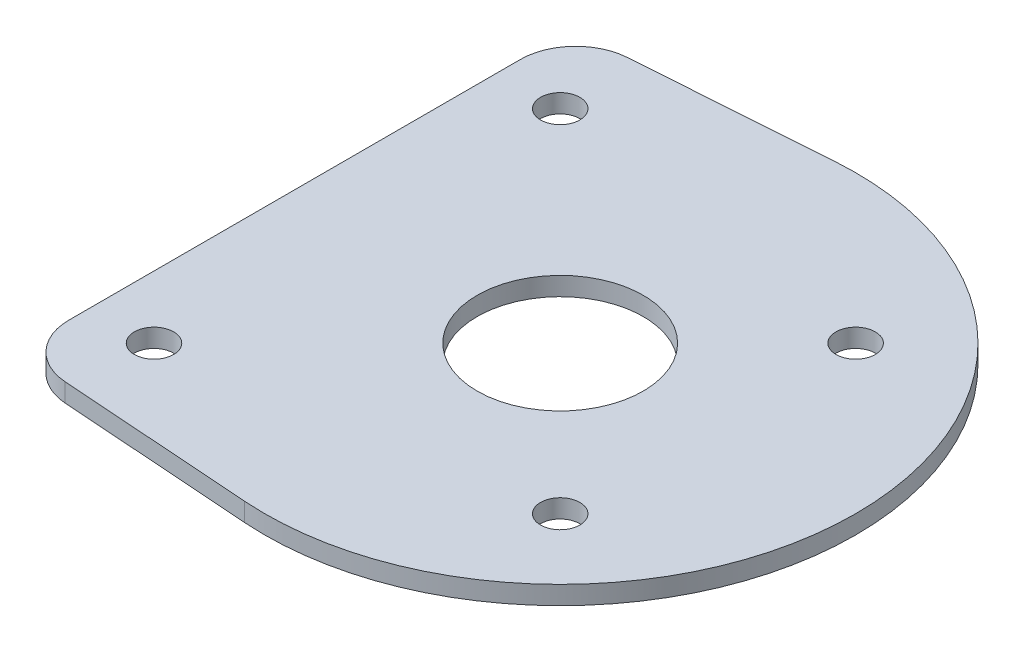
SolidWorks part; units mm, degrees
material "6061 Alloy"
ref_plane "Front Plane" through (0, 0, 0) normal (0, 0, 1) x (1, 0, 0)
ref_plane "Top Plane" through (0, 0, 0) normal (0, 1, 0) x (1, 0, 0)
ref_plane "Right Plane" through (0, 0, 0) normal (1, 0, 0) x (0, 0, -1)
sketch "Sketch1" plane through (0, 0, 0) normal (0, 1, 0) x (1, 0, 0)
  line L0 (87.0156, 23.109) -> (-1.4599, 13.6381) construction
  line L1 (-17.9605, -17.9605) -> (17.9605, -17.9605) construction
  line L2 (-17.9605, -17.9605) -> (-17.9605, 17.9605) construction
  line L3 (-17.9605, 17.9605) -> (17.9605, 17.9605) construction
  line L4 (17.9605, -17.9605) -> (17.9605, 17.9605) construction
  line L5 (-17.9605, -17.9605) -> (17.9605, 17.9605) construction
  line L6 (-17.9605, 17.9605) -> (17.9605, -17.9605) construction
  line L7 (87.0156, -23.109) -> (-1.4599, -13.6381) construction
  line L8 (85.8846, 50.6719) -> (-3.1541, 44.338)
  line L9 (85.8846, -50.6719) -> (-3.1541, -44.338)
  circle A1 centre (0, 0) radius 13.716 construction
  circle A2 centre (89.4893, 0) radius 23.241 construction
  circle A3 centre (89.4893, 0) radius 14.2812
  circle A4 centre (0, 0) radius 19.177
  arc A5 (-3.1541, 44.338) -> (-3.1541, -44.338) centre (0, 0) ccw
  arc A6 (85.8846, 50.6719) -> (85.8846, -50.6719) centre (89.4893, 0) cw
  point P0 (0, 0)
  point P2 (140.2893, 0)
  point P27 (-44.45, 0)
  dimension "D1" = 50.8
  dimension "D2" = 27.432
  dimension "D3" = 46.482
  dimension "D5" = 28.5623
  dimension "D6" = 38.354
  dimension "D4" = 89.4893
  dimension "D7" = 44.45
  dimension "D8" = 50.8
extrude "Boss-Extrude1" add sketch "Sketch1" along normal blind 3.175
hole_wizard "#10 Clearance Hole1" positions "Sketch2" profile "Sketch3" hole size "#10" standard "ANSI Inch" end condition through all
sketch "Sketch2" plane through (0, 3.175, 0) normal (0, 1, 0) x (1, 0, 0)
  line L0 (-44.45, 0) -> (-19.177, 0) construction
  line L1 (-3.1541, -44.338) -> (85.8846, -50.6719) construction
  arc A0 (-3.1541, 44.338) -> (-3.1541, -44.338) centre (0, 0) ccw construction
  circle A1 centre (0, 0) radius 19.177 construction
  point P0 (-17.9605, 17.9605)
  point P3 (17.9605, 17.9605)
  point P6 (17.9605, -17.9605)
  point P9 (-17.9605, -17.9605)
  point P12 (-31.8135, 0)
  point P14 (34.925, 34.3147)
  point P16 (34.925, -34.3147)
  dimension "D1" = 12.7
  dimension "D2" = 34.925
sketch "Sketch3" plane through (-17.9605, 3.175, -17.9605) normal (1, 0, 0) x (0, 0, 1)
  line L0 (0, 0) -> (0, 3.175)
  line L1 (0, 3.175) -> (2.5527, 3.175)
  line L2 (2.5527, 3.175) -> (2.5527, 0)
  line L5 (2.5527, 0) -> (0, 0)
  line L11 (0, -6.35) -> (0, 107.95) construction
  dimension "Thru Hole Dia." = 5.1054
  dimension "Thru Hole Depth" = 3.175
hole_wizard "1/4 Clearance Hole1" positions "Sketch4" profile "Sketch5" hole size "1/4" standard "ANSI Inch" end condition through all
sketch "Sketch4" plane through (0, 3.175, 0) normal (0, 1, 0) x (1, 0, 0)
  line L0 (-31.8135, 0) -> (126.5098, 0) construction
  line L1 (140.2893, 0) -> (112.7303, 0) construction
  line L2 (-19.177, 0) -> (-44.45, 0) construction
  arc A0 (85.8846, -50.6719) -> (85.8846, 50.6719) centre (89.4893, 0) ccw construction
  circle A1 centre (89.4893, 0) radius 23.241 construction
  circle A2 centre (0, 0) radius 19.177 construction
  arc A3 (-3.1541, 44.338) -> (-3.1541, -44.338) centre (0, 0) ccw construction
  circle A5 centre (89.4893, 0) radius 14.2812 construction
  point P4 (54.5643, 34.925)
  point P6 (54.5643, -34.925)
  point P54 (114.8893, 25.4)
  point P56 (114.8893, -25.4)
  dimension "D1" = 34.925
  dimension "D3" = 25.4
  dimension "D2" = 25.4
  dimension "D4" = 34.925
sketch "Sketch5" plane through (54.5643, 3.175, -34.925) normal (1, 0, 0) x (0, 0, 1)
  line L0 (0, 0) -> (0, 3.175)
  line L1 (0, 3.175) -> (3.3782, 3.175)
  line L2 (3.3782, 3.175) -> (3.3782, 0)
  line L5 (3.3782, 0) -> (0, 0)
  line L11 (0, -6.35) -> (0, 107.95) construction
  dimension "Thru Hole Dia." = 6.7564
  dimension "Thru Hole Depth" = 3.175
sketch "Sketch6" plane through (0, 3.175, 0) normal (0, 1, 0) x (1, 0, 0)
  line L0 (-14.3684, 21.5526) -> (-9.4837, 16.6679)
  line L1 (-21.5526, 14.3684) -> (-16.6679, 9.4837)
  line L2 (-17.9605, -17.9605) -> (17.9605, 17.9605) construction
  line L3 (21.5526, -14.3684) -> (16.6679, -9.4837)
  line L4 (14.3684, -21.5526) -> (9.4837, -16.6679)
  arc A0 (-21.5526, 14.3684) -> (-14.3684, 21.5526) centre (-17.9605, 17.9605) cw
  circle A1 centre (0, 0) radius 19.177 construction
  arc A2 (-16.6679, 9.4837) -> (-9.4837, 16.6679) centre (0, 0) cw
  arc A3 (14.3684, -21.5526) -> (21.5526, -14.3684) centre (17.9605, -17.9605) ccw
  arc A4 (9.4837, -16.6679) -> (16.6679, -9.4837) centre (0, 0) ccw
  circle M7 centre (-17.9605, 17.9605) radius 2.5527
  circle M9 centre (17.9605, -17.9605) radius 2.5527
  circle M16 centre (0, 0) radius 19.177
  dimension "D1" = 5.08
extrude "Cut-Extrude1" cut sketch "Sketch6" against normal through all contours A0 L1 L0 M16 M7 | L4 A3 L3 M16 M9
fillet "Fillet1" radius 7.62 4 edges at (-16.6679, 1.5875, -9.4837) (-9.4837, 1.5875, -16.6679) (9.4837, 1.5875, 16.6679) (16.6679, 1.5875, 9.4837)
sketch "Sketch7" plane through (0, 3.175, 0) normal (0, 1, 0) x (1, 0, 0)
  line L0 (43.815, 47.6792) -> (43.815, -47.6792)
  line L1 (85.8846, 50.6719) -> (-3.1541, 44.338) construction
  line L2 (-3.1541, -44.338) -> (85.8846, -50.6719) construction
  line L3 (43.815, -47.6792) -> (-626.425, 0)
  line L4 (-626.425, 0) -> (43.815, 47.6792)
  circle A1 centre (34.925, -34.3147) radius 2.5527 construction
  dimension "D1" = 8.89
extrude "Cut-Extrude2" cut sketch "Sketch7" against normal through all
fillet "Fillet2" radius 9.525 2 edges at (43.815, 1.5875, 47.6792) (43.815, 1.5875, -47.6792)
sketch "Sketch8" [suppressed] plane through (0, 3.175, 0) normal (0, 1, 0) x (1, 0, 0)
  circle A0 centre (89.4893, 0) radius 14.6622
  dimension "D1" = 29.3243
extrude "Cut-Extrude3" [suppressed] cut sketch "Sketch8" against normal through all
